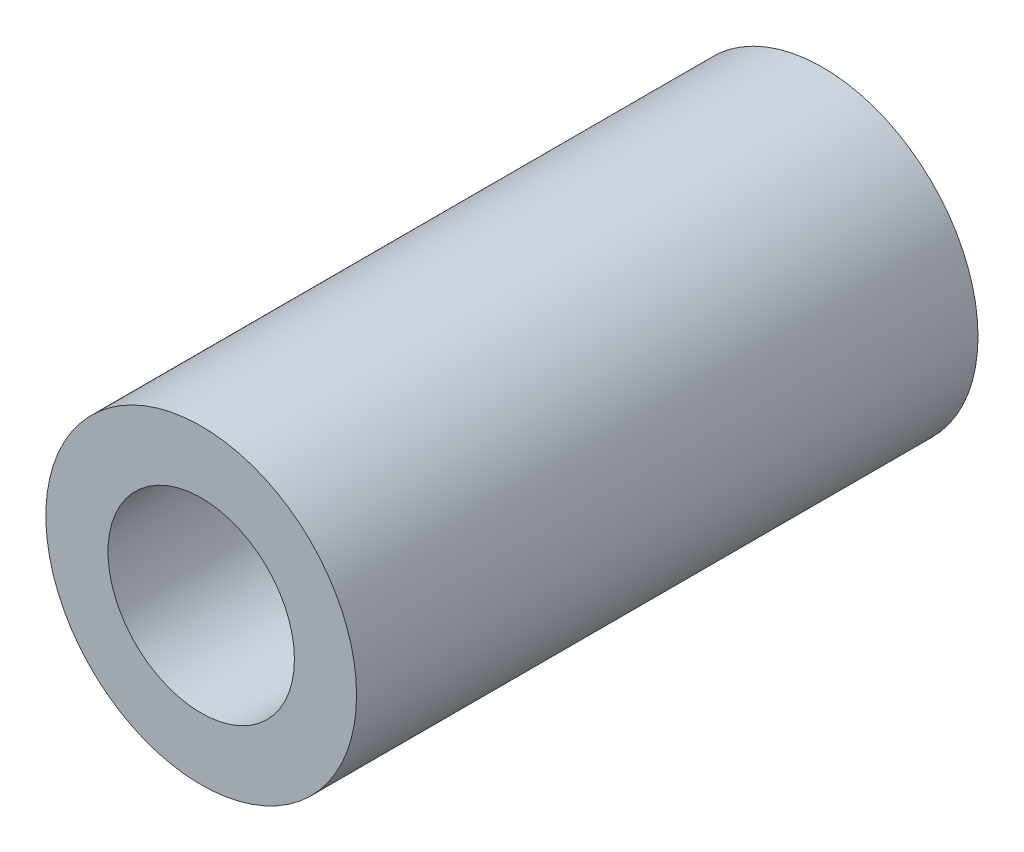
SolidWorks part; units mm, degrees
ref_plane "Front Plane" through (0, 0, 0) normal (0, 0, 1) x (1, 0, 0)
ref_plane "Top Plane" through (0, 0, 0) normal (0, 1, 0) x (1, 0, 0)
ref_plane "Right Plane" through (0, 0, 0) normal (1, 0, 0) x (0, 0, -1)
sketch "Sketch1" plane through (0, 0, 0) normal (0, 0, 1) x (1, 0, 0)
  circle A0 centre (0, 0) radius 2.5
  dimension "D1" = 5
extrude "Boss-Extrude1" add sketch "Sketch1" along normal blind 10
sketch "Sketch2" plane through (0, 0, 10) normal (0, 0, 1) x (1, 0, 0)
  circle A0 centre (0, 0) radius 1.5
  dimension "D1" = 3
extrude "Cut-Extrude1" cut sketch "Sketch2" against normal blind 10
